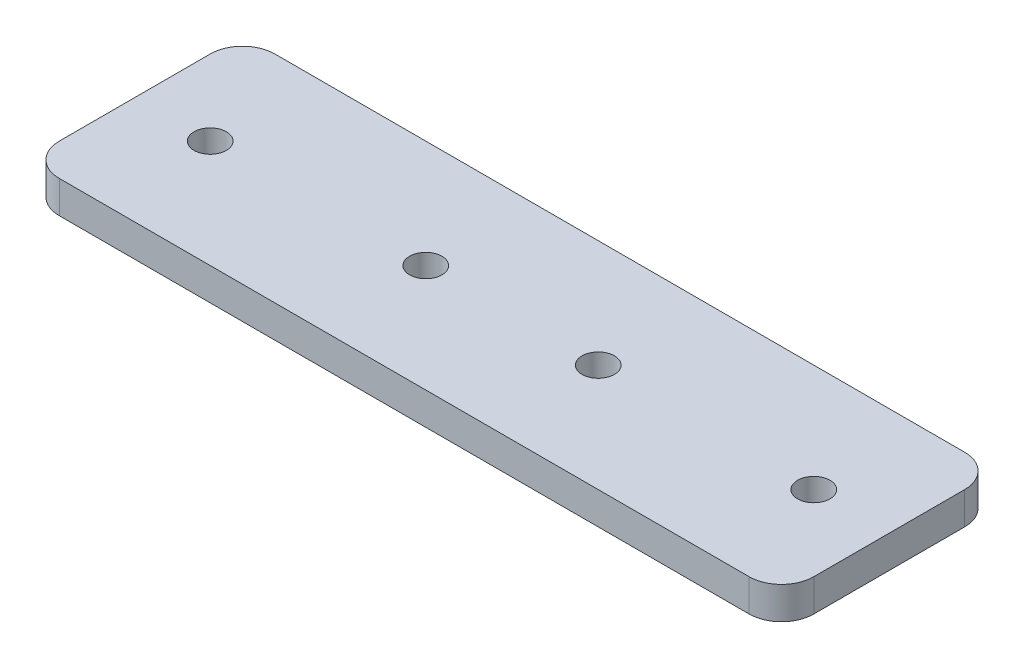
SolidWorks part; units mm, degrees
ref_plane "Front Plane" through (0, 0, 0) normal (0, 0, 1) x (1, 0, 0)
ref_plane "Top Plane" through (0, 0, 0) normal (0, 1, 0) x (1, 0, 0)
ref_plane "Right Plane" through (0, 0, 0) normal (1, 0, 0) x (0, 0, -1)
sketch "Sketch1" plane through (0, 0, 0) normal (0, 1, 0) x (1, 0, 0)
  line L1 (-32, 10) -> (32, 10)
  line L2 (-35, 7) -> (-35, -7)
  line L3 (-32, -10) -> (32, -10)
  line L4 (35, 7) -> (35, -7)
  line L5 (-35, 10) -> (35, -10) construction
  line L6 (-35, -10) -> (35, 10) construction
  arc A0 (35, 7) -> (32, 10) centre (32, 7) ccw
  arc A1 (35, -7) -> (32, -10) centre (32, -7) cw
  arc A2 (-35, -7) -> (-32, -10) centre (-32, -7) ccw
  arc A3 (-35, 7) -> (-32, 10) centre (-32, 7) cw
  circle A4 centre (8, 0) radius 1.5
  circle A5 centre (-8, 0) radius 1.5
  circle A6 centre (28, 0) radius 1.5
  circle A7 centre (-28, 0) radius 1.5
  point P0 (0, 0)
  dimension "D3" = 3
  dimension "D4" = 16
  dimension "D6" = 7
  dimension "D7" = 7
  dimension "D1" = 20
  dimension "D2" = 70
  dimension "D5" = 8
extrude "Boss-Extrude1" add sketch "Sketch1" along normal blind 3
